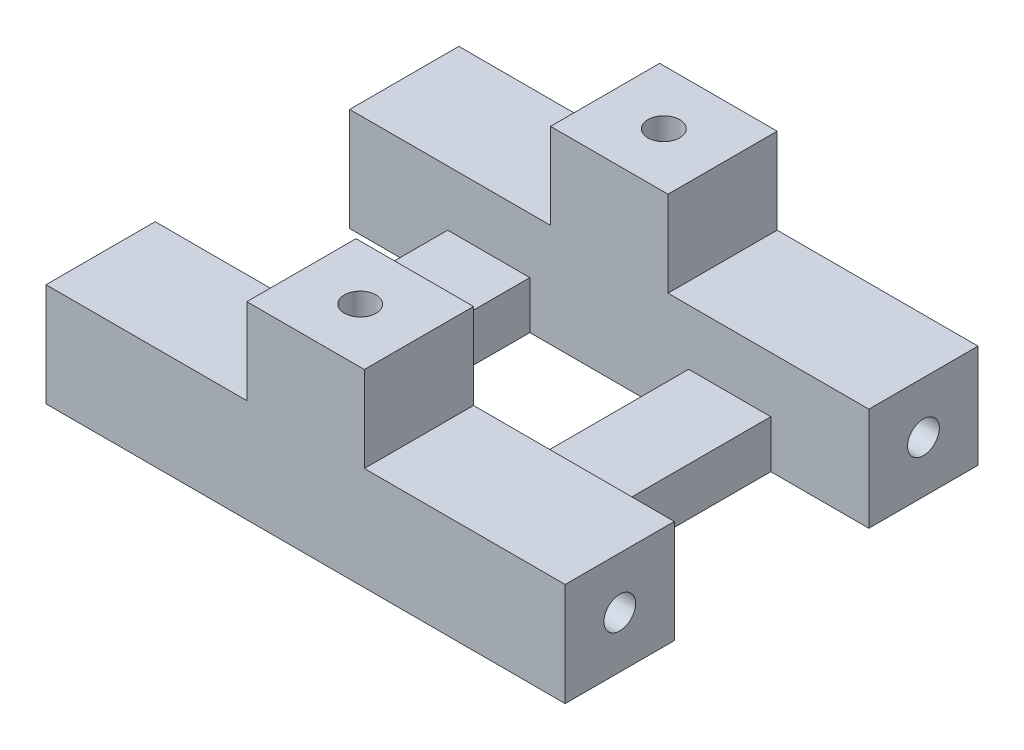
SolidWorks part; units mm, degrees
ref_plane "Alzado" through (0, 0, 0) normal (0, 0, 1) x (1, 0, 0)
ref_plane "Planta" through (0, 0, 0) normal (0, 1, 0) x (1, 0, 0)
ref_plane "Vista lateral" through (0, 0, 0) normal (1, 0, 0) x (0, 0, -1)
sketch "Croquis1" plane through (0, 0, 0) normal (0, 1, 0) x (1, 0, 0)
  line L0 (-15.6068, 13.6193) -> (-15.6068, 6.7443)
  line L1 (-15.6068, 6.7443) -> (-9.4318, 6.7443)
  line L2 (-9.4318, 6.7443) -> (-9.4318, -5.5057)
  line L3 (-9.4318, -5.5057) -> (-15.6068, -5.5057)
  line L4 (-15.6068, -5.5057) -> (-15.6068, -12.3807)
  line L5 (-15.6068, -12.3807) -> (17.0932, -12.3807)
  line L6 (17.0932, -12.3807) -> (17.0932, -5.5057)
  line L7 (17.0932, -5.5057) -> (10.9182, -5.5057)
  line L8 (10.9182, -5.5057) -> (10.9182, 6.7443)
  line L9 (10.9182, 6.7443) -> (17.0932, 6.7443)
  line L10 (17.0932, 6.7443) -> (17.0932, 13.6193)
  line L11 (17.0932, 13.6193) -> (-15.6068, 13.6193)
  line L12 (-4.2568, 6.7443) -> (5.7432, 6.7443)
  line L13 (-4.2568, 6.7443) -> (-4.2568, -5.5057)
  line L14 (-4.2568, -5.5057) -> (5.7432, -5.5057)
  line L15 (5.7432, 6.7443) -> (5.7432, -5.5057)
extrude "Saliente-Extruir1" add sketch "Croquis1" along normal blind 6.5
sketch "Croquis2" plane through (0, 6.5, 0) normal (0, 1, 0) x (1, 0, 0)
  line L0 (-4.2568, -5.5057) -> (5.7432, -5.5057) construction
  line L1 (-2.9568, -5.5057) -> (4.4432, -5.5057)
  line L2 (-2.9568, -5.5057) -> (-2.9568, -12.3807)
  line L3 (-2.9568, -12.3807) -> (4.4432, -12.3807)
  line L4 (4.4432, -5.5057) -> (4.4432, -12.3807)
  line L5 (-15.6068, -12.3807) -> (17.0932, -12.3807) construction
  line L6 (17.0932, 13.6193) -> (-15.6068, 13.6193) construction
  line L7 (-2.9568, 13.6193) -> (4.4432, 13.6193)
  line L8 (-2.9568, 13.6193) -> (-2.9568, 6.7443)
  line L9 (-2.9568, 6.7443) -> (4.4432, 6.7443)
  line L10 (4.4432, 13.6193) -> (4.4432, 6.7443)
  line L11 (5.7432, 6.7443) -> (-4.2568, 6.7443) construction
  circle A0 centre (0.7432, 10.1818) radius 1
  circle A1 centre (0.7432, -8.9432) radius 1
  point P16 (0.7432, 13.6193)
  point P17 (0.7432, 13.6193)
  dimension "D2" = 2
  dimension "D1" = 7.4
extrude "Saliente-Extruir2" add sketch "Croquis2" along normal blind 5.4
sketch "Croquis3" plane through (-15.6068, 0, 0) normal (-1, 0, 0) x (0, 0, 1)
  line L0 (5.5057, 6.5) -> (5.5057, 0) construction
  line L1 (-6.7443, 6.5) -> (5.5057, 6.5)
  line L2 (-6.7443, 6.5) -> (-6.7443, 3)
  line L3 (-6.7443, 3) -> (5.5057, 3)
  line L4 (5.5057, 6.5) -> (5.5057, 3)
  circle A0 centre (-10.1818, 3.25) radius 1
  circle A1 centre (8.9432, 3.25) radius 1
  dimension "D1" = 2
  dimension "D2" = 3.5
extrude "Cortar-Extruir1" cut sketch "Croquis3" against normal blind 35.4
